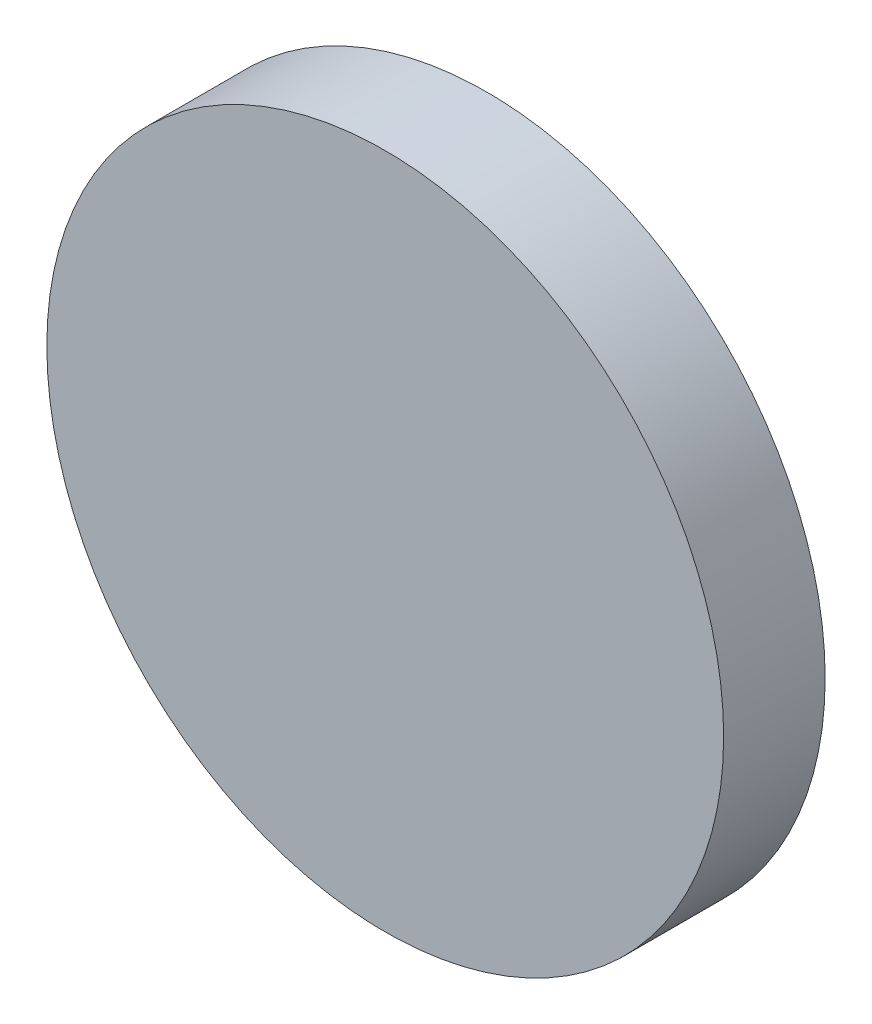
SolidWorks part; units mm, degrees
ref_plane "前视基准面" through (0, 0, 0) normal (0, 0, 1) x (1, 0, 0)
ref_plane "上视基准面" through (0, 0, 0) normal (0, 1, 0) x (1, 0, 0)
ref_plane "右视基准面" through (0, 0, 0) normal (1, 0, 0) x (0, 0, -1)
sketch "草图1" plane through (0, 0, 0) normal (0, 0, 1) x (1, 0, 0)
  circle A0 centre (0, 0) radius 10
  dimension "D1" = 20
extrude "凸台-拉伸1" add sketch "草图1" along normal blind 3 contours A0
